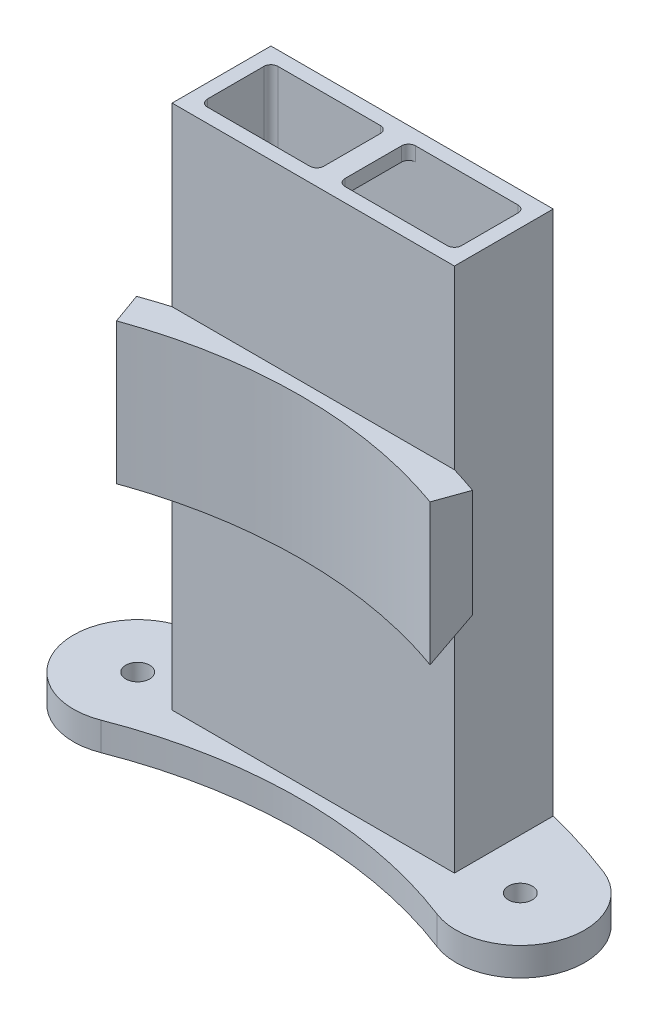
SolidWorks part; units mm, degrees
ref_plane "Front Plane" through (0, 0, 0) normal (0, 0, 1) x (1, 0, 0)
ref_plane "Top Plane" through (0, 0, 0) normal (0, 1, 0) x (1, 0, 0)
ref_plane "Right Plane" through (0, 0, 0) normal (1, 0, 0) x (0, 0, -1)
sketch "Sketch1" plane through (0, 0, 0) normal (0, 1, 0) x (1, 0, 0)
  line L1 (0, 0) -> (36, 0)
  line L2 (0, 0) -> (0, 10)
  line L3 (0, 10) -> (36, 10)
  line L4 (36, 0) -> (36, 10)
  line L5 (-2, -2) -> (38, -2)
  line L6 (-2, -2) -> (-2, 12)
  line L7 (-2, 12) -> (38, 12)
  line L8 (38, -2) -> (38, 12)
  dimension "D1" = 36
  dimension "D2" = 10
  dimension "D3" = 2
  dimension "D4" = 2
  dimension "D5" = 2
  dimension "D6" = 2
extrude "Boss-Extrude1" add sketch "Sketch1" along normal blind 78.5
sketch "Sketch2" plane through (0, 78.5, 0) normal (0, 1, 0) x (1, 0, 0)
  line L0 (36, 10) -> (0, 10) construction
  line L1 (16.5, 0) -> (19.5, 0)
  line L2 (16.5, 0) -> (16.5, 10)
  line L3 (16.5, 10) -> (19.5, 10)
  line L4 (19.5, 0) -> (19.5, 10)
  line L5 (0, 10) -> (36, 0) construction
  line L6 (16.5, 0) -> (19.5, 10) construction
  line L7 (16.5, 10) -> (19.5, 0) construction
  point P1 (18, 5)
  dimension "D1" = 3
extrude "Boss-Extrude2" add sketch "Sketch2" against normal blind 2
sketch "Sketch17" plane through (0, 78.5, 0) normal (0, 1, 0) x (1, 0, 0)
  line L0 (18, -2) -> (18, -69.55) construction
  line L1 (-2, -2) -> (38, -2) construction
  line L2 (-4.2142, -7.6663) -> (-5.8016, -3.244)
  line L3 (18, -69.55) -> (41.8016, -3.244) construction
  line L4 (-2, -2) -> (38, -2)
  line L5 (41.8016, -3.244) -> (40.2142, -7.6663)
  line L6 (-5.8016, -3.244) -> (18, -69.55) construction
  arc A0 (40.2142, -7.6663) -> (-4.2142, -7.6663) centre (18, -69.55) ccw
  arc A1 (-2, -2) -> (-5.8016, -3.244) centre (18, -69.55) ccw
  arc A2 (41.8016, -3.244) -> (38, -2) centre (18, -69.55) ccw
  dimension "D4" = 65.75
  dimension "D1" = 67.55
  dimension "D2" = 4
  dimension "D3" = 4
extrude "Boss-Extrude7" add sketch "Sketch17" against normal blind 20 from offset 25 offset against normal yes
sketch "Sketch19" plane through (-6.171, 0, 2.2152) normal (-0.9412, 0, 0.3379) x (0.3379, 0, 0.9412)
  line L0 (1.0931, 38.1986) -> (5.7917, 33.5)
  line L1 (1.0931, 33.5) -> (5.7917, 33.5)
  line L2 (1.0931, 33.5) -> (1.0931, 38.1986)
  line L3 (1.0931, 38.1986) -> (5.7917, 38.1986) construction
  line L4 (5.7917, 33.5) -> (5.7917, 38.1986) construction
  line L5 (5.7917, 33.5) -> (5.7917, 53.5) construction
  line L6 (5.7917, 33.5) -> (71.5417, 33.5) construction
  line L7 (71.5417, 33.5) -> (71.5417, 85.0632) construction
  dimension "D1" = 65.75
revolve "Cut-Revolve1" cut sketch "Sketch19" angle 323.76 about L7 other way angle 3.31
sketch "Sketch20" plane through (0, 0, 0) normal (0, -1, 0) x (1, 0, 0)
  line L0 (18, 2) -> (18, 69.55) construction
  line L1 (-2, 2) -> (38, 2) construction
  line L2 (0, -10) -> (0, 0) construction
  line L3 (36, 0) -> (36, -10) construction
  line L4 (-2, -12) -> (38, -12) construction
  arc A0 (-5.8099, 8.2626) -> (41.8099, 8.2626) centre (18, 69.55) ccw
  arc A1 (-12.4067, -8.7177) -> (-2, -12) centre (18, 69.55) ccw
  arc A2 (-5.8099, 8.2626) -> (-12.4067, -8.7177) centre (-9.1083, -0.2276) ccw
  arc A3 (48.4067, -8.7177) -> (41.8099, 8.2626) centre (45.1083, -0.2276) ccw
  arc A4 (38, -12) -> (48.4067, -8.7177) centre (18, 69.55) ccw
  circle A5 centre (45.1083, -0.2276) radius 1.7
  circle A6 centre (-9.1083, -0.2276) radius 1.7
  point P6 (18, 2)
  line M1 (-2, 2) -> (-2, -12)
  line M3 (38, -12) -> (38, 2)
  line M4 (38, 2) -> (-2, 2)
  dimension "D2" = 131.5
  dimension "D3" = 3.4
  dimension "D4" = 3.4
  dimension "D1" = 67.55
extrude "Boss-Extrude8" add sketch "Sketch20" along direction (0, -1, 0) on the side against the normal blind 4 separate body contours A4 A3 A0 A2 A1 A6 A5 M3 M1 M4
fillet "Fillet1" radius 1 8 edges at (16.5, 77.5, -10) (19.5, 77.5, 0) (19.5, 77.5, -10) (0, 39.25, -10) (36, 39.25, 0) (16.5, 77.5, 0) (0, 39.25, 0) (36, 39.25, -10)
